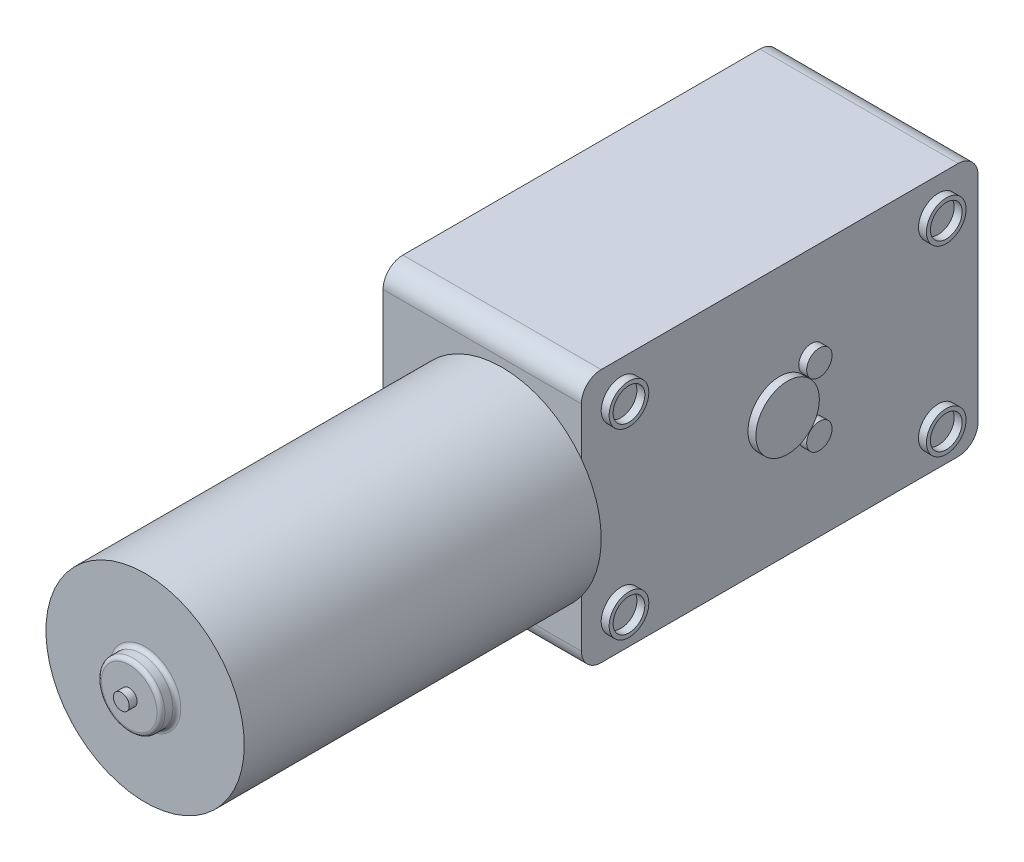
SolidWorks part; units mm, degrees
ref_plane "Front Plane" through (0, 0, 0) normal (0, 0, 1) x (1, 0, 0)
ref_plane "Top Plane" through (0, 0, 0) normal (0, 1, 0) x (1, 0, 0)
ref_plane "Right Plane" through (0, 0, 0) normal (1, 0, 0) x (0, 0, -1)
ref_plane "Plane1" through (83.9692, 0, 0) normal (1, 0, 0) x (0, 0, -1)
sketch "Sketch4" plane through (83.9692, 0, 0) normal (1, 0, 0) x (0, 0, -1)
  line L0 (-28, 7.3) -> (-28, 17.0607) construction
  line L1 (-53, 23.3) -> (-3, 23.3)
  line L2 (-53, 23.3) -> (-53, -8.7)
  line L3 (-53, -8.7) -> (-3, -8.7)
  line L4 (-3, 23.3) -> (-3, -8.7)
  line L5 (-28, 17.0607) -> (-28, 7.3) construction
  line L6 (-28, 7.3) -> (-19.3836, 7.3) construction
  dimension "D1" = 50
  dimension "D2" = 32
extrude "Boss-Extrude1" add sketch "Sketch4" along normal blind 25
sketch "Sketch2" plane through (108.9692, 0, 0) normal (1, 0, 0) x (0, 0, -1)
  circle A0 centre (-8, -4.2) radius 2 construction
  circle A1 centre (-48, -4.2) radius 2 construction
  circle A2 centre (-8, 18.8) radius 2 construction
  circle A3 centre (-48, 18.8) radius 2 construction
  circle A4 centre (-8, -4.2) radius 2
  circle A5 centre (-48, -4.2) radius 2
  circle A6 centre (-8, 18.8) radius 2
  circle A7 centre (-48, 18.8) radius 2
  circle A8 centre (-48, 18.8) radius 2.5
  circle A9 centre (-8, 18.8) radius 2.5
  circle A10 centre (-8, -4.2) radius 2.5
  circle A11 centre (-48, -4.2) radius 2.5
  dimension "D1" = 5
  dimension "D2" = 5
  dimension "D3" = 5
  dimension "D4" = 5
sketch "Sketch5" plane through (83.9692, 0, 0) normal (-1, 0, 0) x (0, 0, 1)
  circle A0 centre (8, 18.8) radius 2
  circle A1 centre (48, 18.8) radius 2
  circle A2 centre (48, -4.2) radius 2
  circle A3 centre (8, -4.2) radius 2
  dimension "D1" = 4
extrude "Cut-Extrude1" cut sketch "Sketch5" against normal blind 5
extrude "Boss-Extrude2" add sketch "Sketch2" along normal blind 1
sketch "Sketch7" plane through (108.9692, 0, 0) normal (1, 0, 0) x (0, 0, -1)
  circle A0 centre (-28, 7.3) radius 4
  circle A1 centre (-24, 11.3) radius 1.6
  circle A2 centre (-24, 3.3) radius 1.6
  dimension "D2" = 3.2
  dimension "D3" = 3.2
extrude "Boss-Extrude3" add sketch "Sketch7" along normal blind 1
fillet "Fillet1" radius 2.5 4 edges at (96.4692, 23.3, 53) (96.4692, 23.3, 3) (96.4692, -8.7, 3) (96.4692, -8.7, 53)
sketch "Sketch8" plane through (0, 0, 53) normal (0, 0, 1) x (1, 0, 0)
  line L2 (83.9692, 7.3) -> (114.4936, 7.3) construction
  line L3 (83.9692, 20.8) -> (83.9692, -6.2) construction
  circle A0 centre (98.9692, 7.3) radius 12.5
  dimension "D1" = 25
  dimension "D2" = 15
extrude "Boss-Extrude4" add sketch "Sketch8" along normal blind 45
sketch "Sketch10" plane through (0, 0, 98) normal (0, 0, 1) x (1, 0, 0)
  line L0 (98.9692, 7.3) -> (115.1254, 7.3) construction
  circle A0 centre (98.9692, 7.3) radius 4
  dimension "D1" = 8
extrude "Boss-Extrude5" add sketch "Sketch10" along normal blind 2
sketch "Sketch11" plane through (0, 0, 100) normal (0, 0, 1) x (1, 0, 0)
  circle A0 centre (98.9692, 7.3) radius 1
  dimension "D1" = 2
extrude "Boss-Extrude6" add sketch "Sketch11" along normal blind 1
fillet "Fillet2" radius 0.5 2 edges at (102.9692, 7.3, 100) (102.9692, 7.3, 98)
